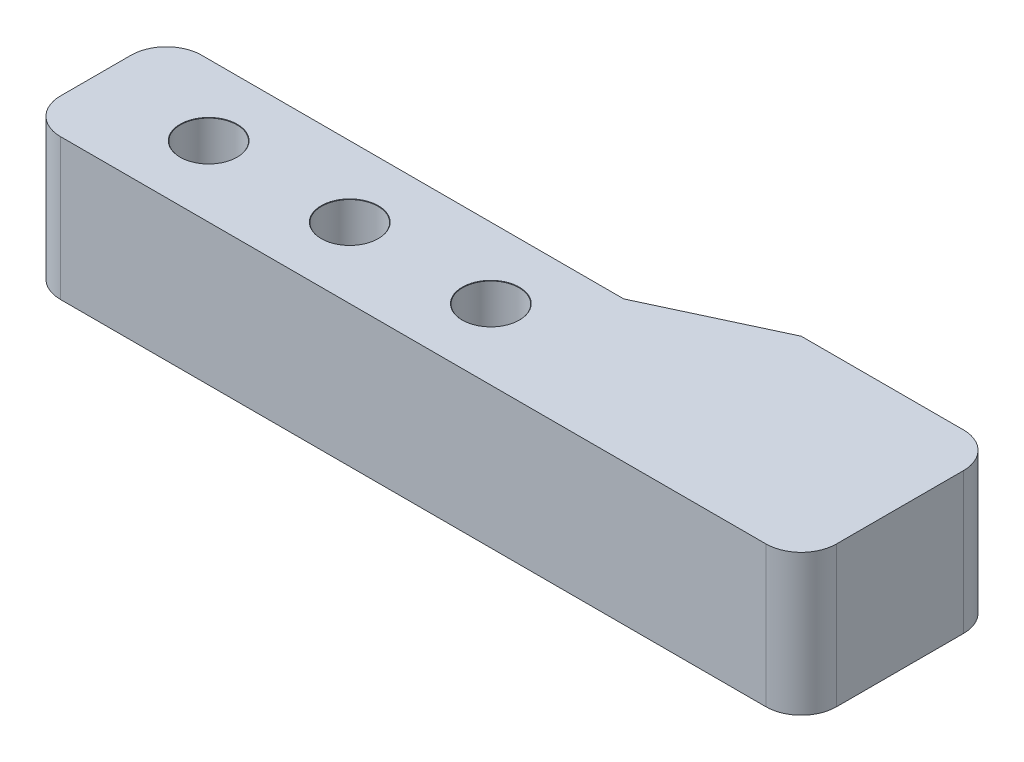
SolidWorks part; units mm, degrees
ref_plane "Front Plane" through (0, 0, 0) normal (0, 0, 1) x (1, 0, 0)
ref_plane "Top Plane" through (0, 0, 0) normal (0, 1, 0) x (1, 0, 0)
ref_plane "Right Plane" through (0, 0, 0) normal (1, 0, 0) x (0, 0, -1)
sketch "Sketch1" plane through (0, 0, 0) normal (0, 1, 0) x (1, 0, 0)
  line L0 (-9.4822, 0) -> (19.3529, 0) construction
  line L1 (0, 5) -> (0, -5)
  line L2 (0, -5) -> (55, -5)
  line L3 (55, -5) -> (55, 9)
  line L4 (55, 9) -> (41, 9)
  line L5 (41, 9) -> (32.422, 5)
  line L6 (32.422, 5) -> (0, 5)
  dimension "D1" = 55
  dimension "D2" = 10
  dimension "D3" = 5
  dimension "D4" = 14
  dimension "D5" = 14
  dimension "D6" = 25
extrude "Boss-Extrude1" add sketch "Sketch1" along normal blind 10
sketch "Sketch2" plane through (0, 10, 0) normal (0, 1, 0) x (1, 0, 0)
  line L0 (-4.2684, 0) -> (42.1691, 0) construction
  line L1 (8, 0) -> (18, 0) construction
  point P3 (8, 0)
  point P6 (18, 0)
  point P7 (28, 0)
  dimension "D1" = 3
  dimension "D2" = 10
  dimension "D3" = 8
hole_wizard "Ø4.0mm Dowel Hole1" positions "Sketch3" profile "Sketch4" hole size "Ø4.0" standard "ANSI Metric" end condition through all
sketch "Sketch3" plane through (0, 10, 0) normal (0, 1, 0) x (1, 0, 0)
  point P0 (8, 0)
  point P3 (18, 0)
  point P6 (28, 0)
sketch "Sketch4" plane through (8, 10, 0) normal (1, 0, 0) x (0, 0, 1)
  line L0 (0, 0) -> (0, 10)
  line L1 (0, 10) -> (2, 10)
  line L2 (2, 10) -> (2, 0.025)
  line L3 (2, 0.025) -> (2.025, 0)
  line L5 (2.025, 0) -> (0, 0)
  line L6 (-2, 0.025) -> (-2.025, 0) construction
  line L11 (0, -6.35) -> (0, 107.95) construction
  dimension "Thru Hole Dia." = 4
  dimension "Thru Hole Depth" = 10
  dimension "Near C'Sink Dia." = 4.05
  dimension "Near C'Sink Angle" = 90
sketch "Sketch5" plane through (0, 0, 0) normal (0, -1, 0) x (1, 0, 0)
  line L0 (-5.6303, 0) -> (43.6492, 0) construction
  line L1 (-4.2684, 0) -> (42.1691, 0) construction
  line L2 (9.75, -3.0311) -> (11.5, 0)
  line L3 (11.5, 0) -> (9.75, 3.0311)
  line L4 (9.75, 3.0311) -> (6.25, 3.0311)
  line L5 (6.25, 3.0311) -> (4.5, 0)
  line L6 (4.5, 0) -> (6.25, -3.0311)
  line L7 (6.25, -3.0311) -> (9.75, -3.0311)
  line L8 (21.5, 0) -> (19.75, 3.0311)
  line L9 (19.75, 3.0311) -> (16.25, 3.0311)
  line L10 (16.25, 3.0311) -> (14.5, 0)
  line L11 (14.5, 0) -> (16.25, -3.0311)
  line L12 (16.25, -3.0311) -> (19.75, -3.0311)
  line L13 (19.75, -3.0311) -> (21.5, 0)
  line L14 (31.5, 0) -> (29.75, 3.0311)
  line L15 (29.75, 3.0311) -> (26.25, 3.0311)
  line L16 (26.25, 3.0311) -> (24.5, 0)
  line L17 (24.5, 0) -> (26.25, -3.0311)
  line L18 (26.25, -3.0311) -> (29.75, -3.0311)
  line L19 (29.75, -3.0311) -> (31.5, 0)
  line L20 (11.5, 0) -> (21.5, 0) construction
  circle A0 centre (8, 0) radius 3.0311 construction
  circle A1 centre (18, 0) radius 3.0311 construction
  circle A2 centre (28, 0) radius 3.0311 construction
  dimension "D1" = 8
  dimension "D2" = 3.5
  dimension "D4" = 10
  dimension "D3" = 3
extrude "Cut-Extrude1" cut sketch "Sketch5" against normal blind 3
fillet "Fillet1" radius 2.5 4 edges at (55, 5, -9) (55, 5, 5) (0, 5, -5) (0, 5, 5)
